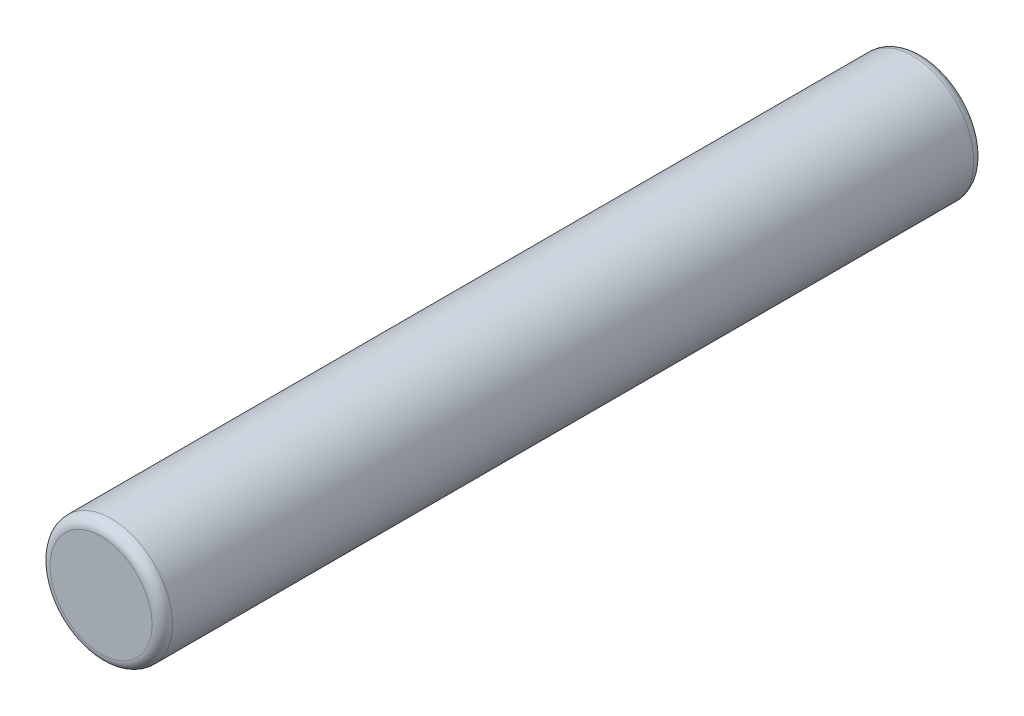
SolidWorks part; units mm, degrees
material "Brass"
ref_plane "Front Plane" through (0, 0, 0) normal (0, 0, 1) x (1, 0, 0)
ref_plane "Top Plane" through (0, 0, 0) normal (0, 1, 0) x (1, 0, 0)
ref_plane "Right Plane" through (0, 0, 0) normal (1, 0, 0) x (0, 0, -1)
sketch "Sketch1" plane through (0, 0, 0) normal (0, 0, 1) x (1, 0, 0)
  circle A0 centre (0, 0) radius 3
extrude "Boss-Extrude1" add sketch "Sketch1" along normal blind 40.3
fillet "Fillet1" radius 0.5 1 edges at (3, 0, 0)
fillet "Fillet2" radius 0.5 1 edges at (3, 0, 40.3)
